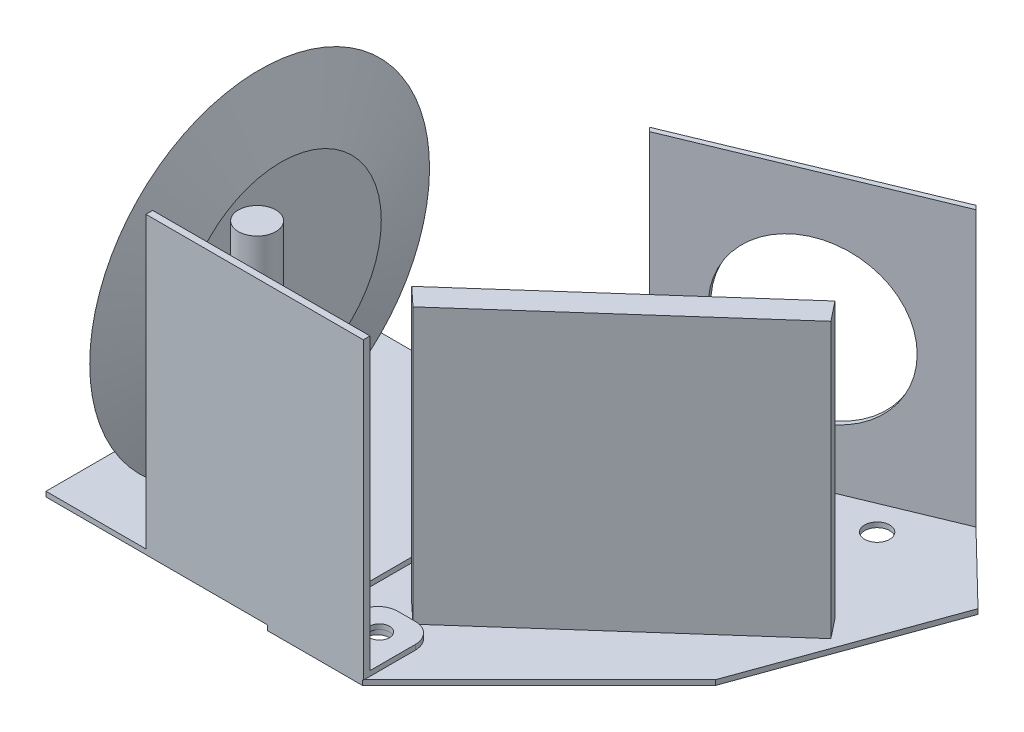
SolidWorks part; units mm, degrees
ref_plane "Alzado" through (0, 0, 0) normal (0, 0, 1) x (1, 0, 0)
ref_plane "Planta" through (0, 0, 0) normal (0, 1, 0) x (1, 0, 0)
ref_plane "Vista lateral" through (0, 0, 0) normal (1, 0, 0) x (0, 0, -1)
sketch "Croquis1" plane through (0, 0, 0) normal (0, 1, 0) x (1, 0, 0)
  line L0 (57.75, 14.4) -> (57.75, 8.9868) construction
  line L1 (0, 0) -> (48, 0)
  line L2 (0, 0) -> (0, 61)
  line L3 (0, 61) -> (43.4174, 61)
  line L4 (48, 5.7871) -> (48, 58)
  line L5 (53, 0) -> (63.5, 0)
  line L6 (52, 5.7871) -> (52, 10.4)
  line L7 (56, 14.4) -> (59.5, 14.4)
  line L8 (63.5, 0) -> (63.5, 10.4)
  line L10 (53, 0) -> (48, 0)
  line L12 (52, 5.7871) -> (48, 5.7871)
  circle A0 centre (48, 63) radius 2
  circle A1 centre (57.75, 8.9868) radius 2
  arc A2 (59.5, 14.4) -> (63.5, 10.4) centre (59.5, 10.4) cw
  arc A3 (52, 10.4) -> (56, 14.4) centre (56, 10.4) cw
  arc A4 (48, 58) -> (43.4174, 61) centre (48, 63) ccw
  point P15 (63.5, 14.4)
  dimension "D3" = 4
  dimension "D6" = 4
  dimension "D7" = 4
  dimension "D10" = 10
  dimension "D2" = 48
  dimension "D4" = 61
  dimension "D5" = 14.4
  dimension "D8" = 11.5
  dimension "D9" = 4
extrude "Saliente-Extruir1" add sketch "Croquis1" along normal blind 1
sketch "Croquis2" plane through (0, 1, 0) normal (0, 1, 0) x (1, 0, 0)
  line L1 (63.5, 0) -> (20, 0)
  line L2 (63.5, 0) -> (63.5, 1.3393)
  line L3 (63.5, 1.3393) -> (20, 1.3393)
  line L4 (20, 0) -> (20, 1.3393)
  dimension "D1" = 43.5
extrude "Saliente-Extruir2" add sketch "Croquis2" along normal blind 58
sketch "Croquis3" plane through (0, 0, 0) normal (0, -1, 0) x (-1, 0, 0)
  line L0 (-44.3009, 65.5) -> (-44.3009, 0)
  line L1 (-44.3009, 65.5) -> (-98.2554, 87.8487)
  line L2 (-44.3009, 0) -> (-63.3009, 0)
  line L3 (-63.3009, 0) -> (-98.6562, 35.3553)
  line L4 (-44.3009, 65.5) -> (-67.3228, 65.5) construction
  line L5 (-98.2554, 87.8487) -> (-112.5996, 73.9116)
  line L6 (-112.5996, 73.9116) -> (-98.6562, 35.3553)
  line L8 (0, 0) -> (-63.5, 0) construction
  line L9 (0, 61) -> (0, 0) construction
  circle A0 centre (-57.8009, 8.5) radius 2.5
  circle A1 centre (-48.4406, 62.8801) radius 2.5
  circle A2 centre (-89.2467, 77.0816) radius 2.5
  dimension "D9" = 5
  dimension "D13" = 5
  dimension "D16" = 5
  dimension "D1" = 65.5
  dimension "D2" = 58.4
  dimension "D3" = 19
  dimension "D4" = 50
  dimension "D5" = 45
  dimension "D6" = 22.5
  dimension "D7" = 20
  dimension "D8" = 41
  dimension "D10" = 13.5
  dimension "D11" = 8.5
  dimension "D12" = 44.3009
  dimension "D14" = 4.1397
  dimension "D15" = 62.8801
  dimension "D17" = 6.5
  dimension "D18" = 14
extrude "Saliente-Extruir3" add sketch "Croquis3" along normal blind 1
sketch "Croquis4" plane through (0, 0, 0) normal (0, 1, 0) x (1, 0, 0)
  line L0 (51.2804, 69.4734) -> (97.4744, 88.6076)
  line L1 (49.6555, 67.718) -> (98.2554, 87.8487) construction
  line L2 (98.2554, 87.8487) -> (112.5996, 73.9116) construction
  line L3 (98.2554, 87.8487) -> (52.0614, 68.7145)
  line L4 (52.0614, 68.7145) -> (51.2804, 69.4734)
  line L5 (98.2554, 87.8487) -> (97.4744, 88.6076)
  dimension "D1" = 50
  dimension "D2" = 1
  dimension "D3" = 50
extrude "Saliente-Extruir4" add sketch "Croquis4" along normal blind 55 separate body
sketch "Croquis5" plane through (-16.67, 0, -40.245) normal (0.3827, 0, 0.9239) x (0.9239, 0, -0.3827)
  line L0 (99.3944, 55) -> (99.3944, 27.5) construction
  line L1 (74.3944, 55) -> (124.3944, 55) construction
  line L2 (124.3944, 27.5) -> (99.3944, 27.5) construction
  line L3 (124.3944, 55) -> (124.3944, 0) construction
  circle A0 centre (99.3944, 27.5) radius 16
  dimension "D1" = 32
extrude "Cortar-Extruir1" cut sketch "Croquis5" against normal blind 55
sketch "Croquis6" plane through (0, 0, 0) normal (0, 1, 0) x (1, 0, 0)
  line L0 (55.0824, 18.1066) -> (99.973, 57.9166)
  line L1 (58.7581, 14.6834) -> (103.0782, 53.9874)
  line L2 (55.0824, 18.1066) -> (58.7581, 14.6834)
  line L3 (99.973, 57.9166) -> (103.0782, 53.9874)
  dimension "D1" = 60
  dimension "D2" = 5
extrude "Saliente-Extruir5" add sketch "Croquis6" along normal blind 55
ref_plane "Plano1" through (10, 0, 0) normal (-1, 0, 0) x (0, 0, 1)
sketch "Croquis7" plane through (10, 0, 0) normal (-1, 0, 0) x (0, 0, 1)
  line L1 (-32.75, -1.3194) -> (-32.75, 37.1512) construction
  line L3 (-65.5, -1) -> (-65.5, 0) construction
  circle A0 centre (-32.75, 28.6806) radius 34
  point P9 (-65.5, -0.5)
  dimension "D3" = 68
  dimension "D1" = 32.75
  dimension "D2" = 30
extrude "Saliente-Extruir6" add sketch "Croquis7" along normal mid plane 8.5 draft 73
sketch "Croquis8" plane through (0, 1, 0) normal (0, 1, 0) x (1, 0, 0)
  line L0 (63.5, 1.3393) -> (63.5, 10.4) construction
  circle A0 centre (32.25, 10) radius 3.75
  point P5 (63.5, 10.4)
  dimension "D1" = 7.5
  dimension "D2" = 10
  dimension "D3" = 31.25
extrude "Saliente-Extruir7" add sketch "Croquis8" along normal up to surface (58 mm away) up to face at (41.75, 59, -0.6697)
